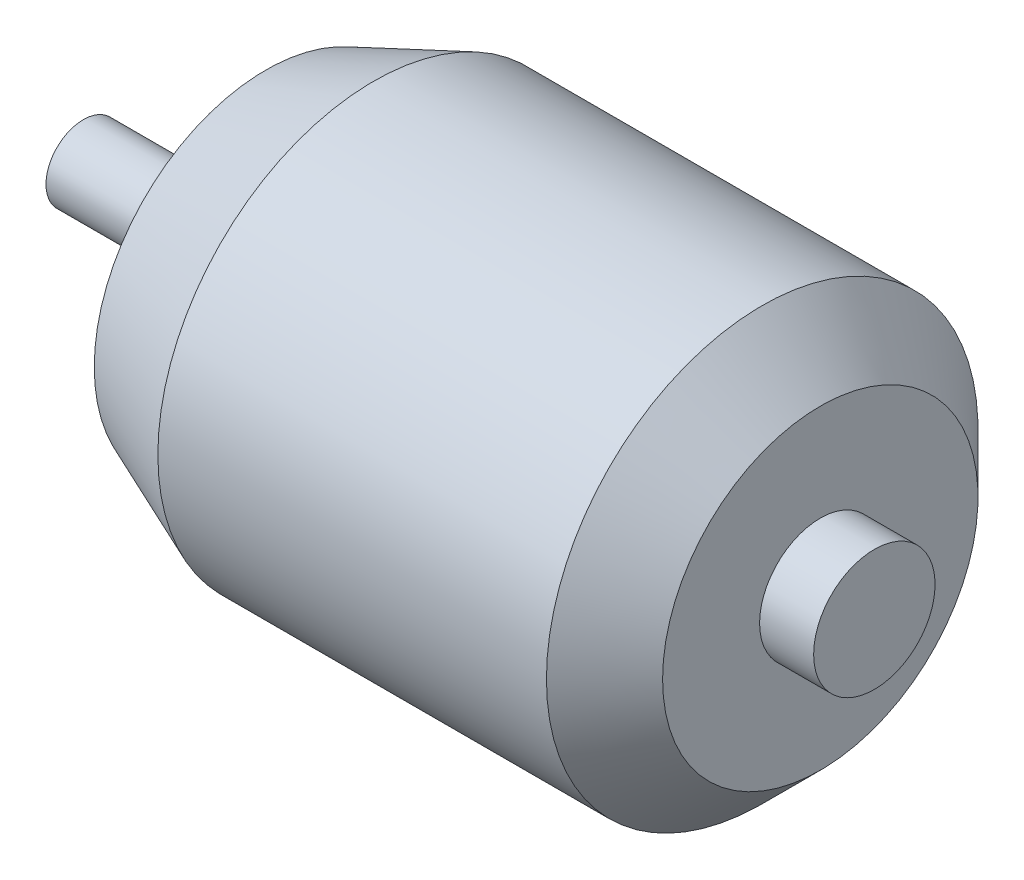
SolidWorks part; units mm, degrees
ref_plane "Front Plane" through (0, 0, 0) normal (0, 0, 1) x (1, 0, 0)
ref_plane "Top Plane" through (0, 0, 0) normal (0, 1, 0) x (1, 0, 0)
ref_plane "Right Plane" through (0, 0, 0) normal (1, 0, 0) x (0, 0, -1)
sketch "Sketch1" plane through (0, 0, 0) normal (0, 0, 1) x (1, 0, 0)
  line L0 (0, 48.1854) -> (0, -65.9735) construction
  line L1 (-68.4229, 0) -> (68.4229, 0) construction
  line L2 (-48.5943, 0) -> (-48.5943, 4.2901)
  line L3 (-48.5943, 4.2901) -> (-27.6756, 4.2901)
  line L4 (-27.6756, 4.2901) -> (-27.6756, 19.6747)
  line L5 (-27.6756, 19.6747) -> (-15.3045, 24.75)
  line L6 (-15.3045, 24.75) -> (29.2631, 24.75)
  line L7 (29.2631, 24.75) -> (35.9244, 18.0887)
  line L8 (35.9244, 18.0887) -> (35.9244, 6.9623)
  line L9 (35.9244, 6.9623) -> (42.1244, 6.9623)
  line L10 (42.1244, 6.9623) -> (42.1244, 0)
  line L11 (42.1244, 0) -> (-48.5943, 0)
  dimension "D1" = 63.6
  dimension "D2" = 6.2
  dimension "D3" = 90.7187
  dimension "D4" = 24.75
revolve "Revolve1" add sketch "Sketch1" angle 360 about L1
